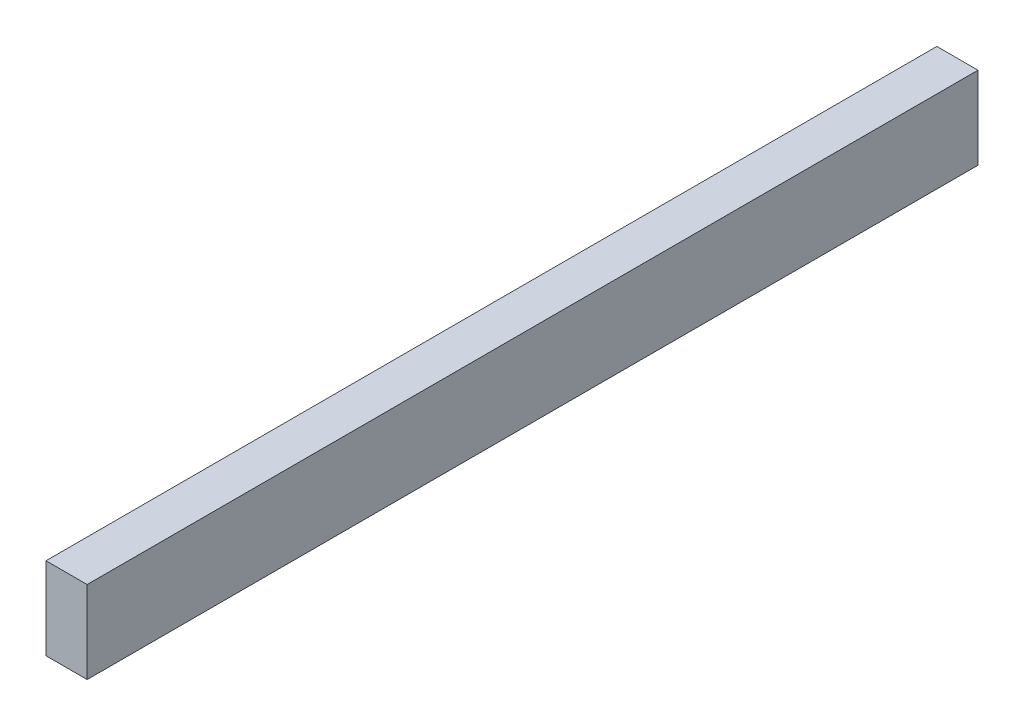
SolidWorks part; units mm, degrees
material "Cedar"
ref_plane "Front Plane" through (0, 0, 0) normal (0, 0, 1) x (1, 0, 0)
ref_plane "Top Plane" through (0, 0, 0) normal (0, 1, 0) x (1, 0, 0)
ref_plane "Right Plane" through (0, 0, 0) normal (1, 0, 0) x (0, 0, -1)
sketch "Sketch1" plane through (0, 0, 0) normal (1, 0, 0) x (0, 0, -1)
  line L1 (-119.1068, -11.7187) -> (293.186, -11.7187)
  line L2 (-119.1068, -11.7187) -> (-119.1068, -49.8187)
  line L3 (-119.1068, -49.8187) -> (293.186, -49.8187)
  line L4 (293.186, -11.7187) -> (293.186, -49.8187)
  dimension "D1" = 412.2928
  dimension "D2" = 38.1
extrude "Boss-Extrude1" add sketch "Sketch1" along normal blind 19.05
